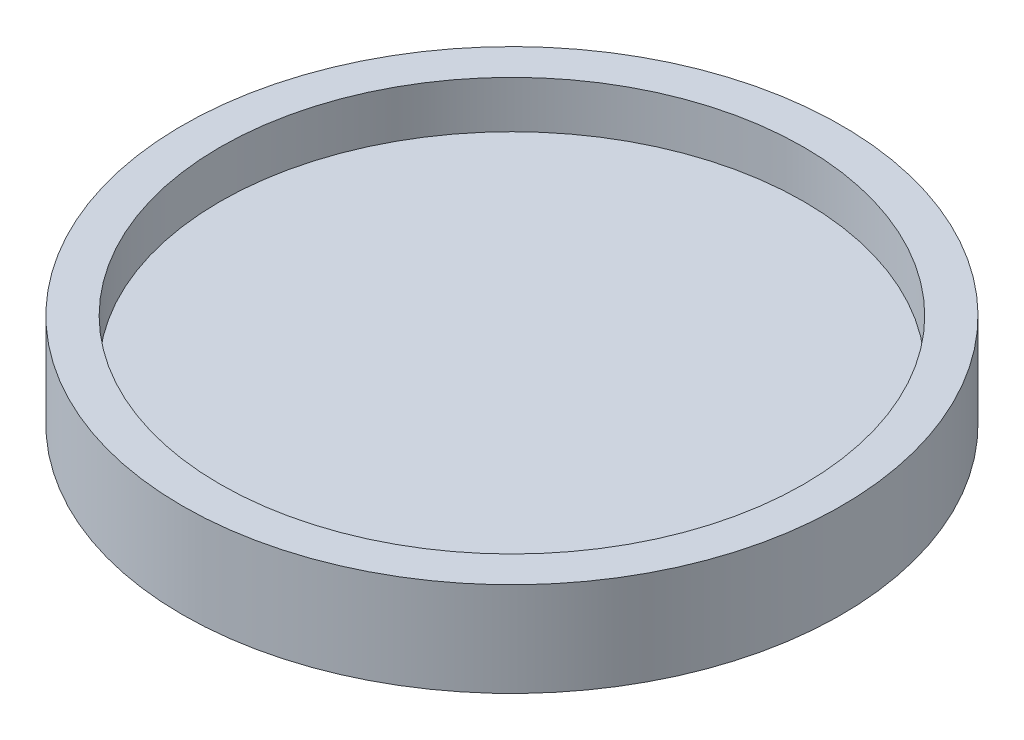
SolidWorks part; units mm, degrees
ref_plane "Front Plane" through (0, 0, 0) normal (0, 0, 1) x (1, 0, 0)
ref_plane "Top Plane" through (0, 0, 0) normal (0, 1, 0) x (1, 0, 0)
ref_plane "Right Plane" through (0, 0, 0) normal (1, 0, 0) x (0, 0, -1)
sketch "Sketch1" plane through (0, 0, 0) normal (0, 1, 0) x (1, 0, 0)
  circle A0 centre (0, 0) radius 35
extrude "Boss-Extrude2" add sketch "Sketch1" along normal blind 10
sketch "Sketch2" plane through (0, 10, 0) normal (0, 1, 0) x (1, 0, 0)
  circle A0 centre (0, 0) radius 31
extrude "Cut-Extrude1" cut sketch "Sketch2" against normal blind 5
sketch "Sketch3" plane through (0, 0, 0) normal (0, -1, 0) x (1, 0, 0)
  circle A0 centre (0, 0) radius 1.5
extrude "Boss-Extrude3" add sketch "Sketch3" along normal blind 5
